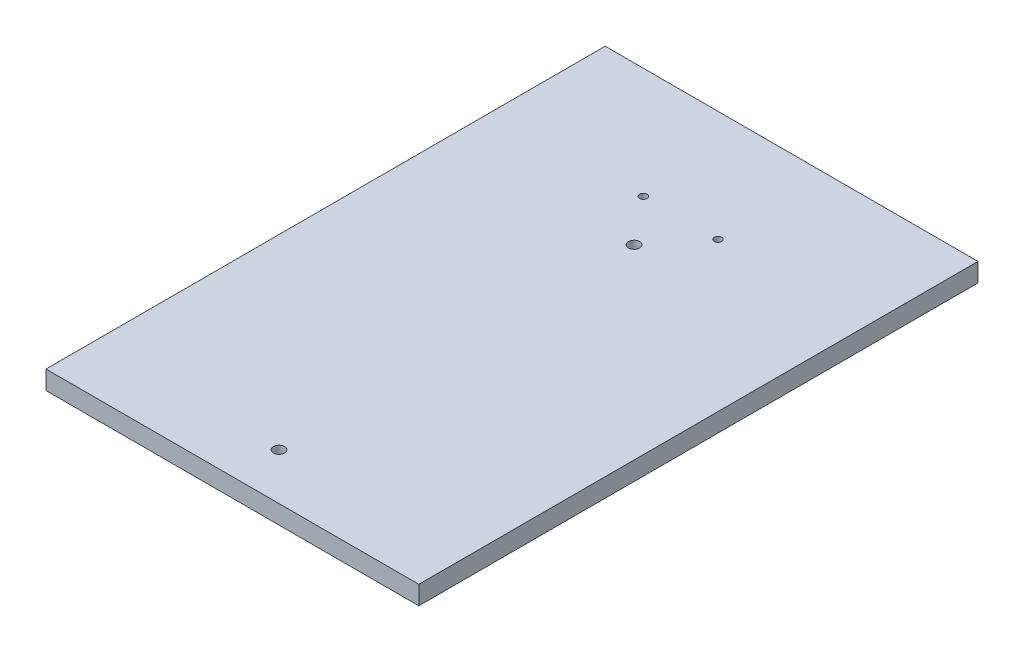
SolidWorks part; units mm, degrees
material "1023 Karbon Çeliği Levha (SS)"
ref_plane "Ön Düzlem" through (0, 0, 0) normal (0, 0, 1) x (1, 0, 0)
ref_plane "Üst Düzlem" through (0, 0, 0) normal (0, 1, 0) x (1, 0, 0)
ref_plane "Sağ Düzlem" through (0, 0, 0) normal (1, 0, 0) x (0, 0, -1)
sketch "Çizim1" plane through (0, 0, 0) normal (0, 1, 0) x (1, 0, 0)
  line L0 (-100, 150) -> (100, -150) construction
  line L1 (-100, 150) -> (100, 150)
  line L2 (-100, 150) -> (-100, -150)
  line L3 (-100, -150) -> (100, -150)
  line L4 (100, 150) -> (100, -150)
  dimension "D1" = 300
  dimension "D2" = 200
extrude "Yükseklik-Ekstrüzyon1" add sketch "Çizim1" along normal blind 10
sketch "Çizim2" plane through (0, 10, 0) normal (0, 1, 0) x (1, 0, 0)
  line L0 (-100, -150) -> (100, -150) construction
  circle A0 centre (0, -125) radius 3
  circle A1 centre (0, 65.5) radius 3
  circle A2 centre (-20, 90.5) radius 2
  circle A3 centre (20, 90.5) radius 2
  dimension "D3" = 40
  dimension "D4" = 20
  dimension "D1" = 190.5
  dimension "D2" = 25
  dimension "D5" = 25
extrude "Kes-Ekstrüzyon1" cut sketch "Çizim2" against normal blind 10
